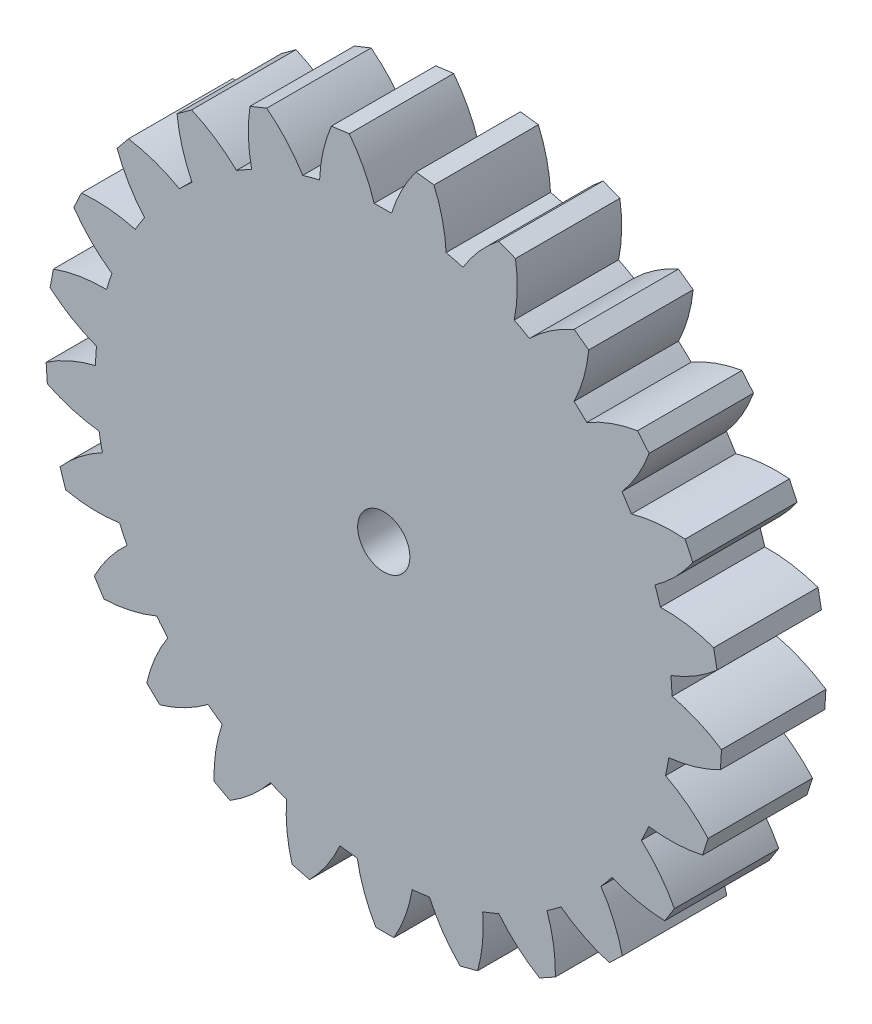
SolidWorks part; units mm, degrees
ref_plane "Front Plane" through (0, 0, 0) normal (0, 0, 1) x (1, 0, 0)
ref_plane "Top Plane" through (0, 0, 0) normal (0, 1, 0) x (1, 0, 0)
ref_plane "Right Plane" through (0, 0, 0) normal (1, 0, 0) x (0, 0, -1)
ref_plane "Plane4"
sketch "Sketch1" plane through (0, 0, 0) normal (0, 0, 1) x (1, 0, 0)
  line L0 (-14.2336, 38.5672) -> (-16.2739, 37.7516)
  line L1 (-4.1952, 40.8953) -> (-6.3742, 40.6127)
  line L2 (6.1069, 40.6538) -> (3.926, 40.922)
  line L3 (16.0252, 37.8579) -> (13.9796, 38.66)
  line L4 (24.9366, 32.6832) -> (23.1547, 33.9689)
  line L5 (32.2811, 25.4549) -> (30.875, 27.1433)
  line L6 (37.5973, 16.6272) -> (36.6553, 18.6123)
  line L7 (40.5512, 6.7547) -> (40.1323, 8.9117)
  line L8 (40.957, -3.5421) -> (41.0878, -1.3488)
  line L9 (38.7894, -13.6165) -> (39.4615, -11.5245)
  line L10 (34.1845, -22.8352) -> (35.3557, -20.9761)
  line L11 (27.4316, -30.6191) -> (29.0284, -29.1097)
  line L12 (18.9551, -36.4791) -> (20.8771, -35.4142)
  line L13 (9.2876, -40.047) -> (11.4141, -39.4936)
  line L14 (-0.9634, -41.0986) -> (1.2338, -41.0914)
  line L15 (-11.154, -39.5678) -> (-9.0239, -40.1073)
  line L16 (-20.6437, -35.5508) -> (-18.7147, -36.6031)
  line L17 (-28.8363, -29.3001) -> (-27.2296, -30.7989)
  line L18 (-35.2169, -21.2083) -> (-34.0335, -23.0596)
  line L19 (-39.3848, -11.7839) -> (-38.699, -13.8714)
  line L20 (-41.078, -1.6191) -> (-40.9328, -3.8115)
  line L21 (-36.7769, 18.3707) -> (-37.7059, 16.3795)
  line L22 (-40.1901, 8.6475) -> (-40.5947, 6.4878)
  line L23 (-23.3777, 33.8158) -> (-25.1511, 32.5184)
  line L24 (-31.0529, 26.9396) -> (-32.4479, 25.2419)
  line L25 (-17.9243, 30.1668) -> (-23.3244, 26.2162)
  line L26 (-24.8633, 24.7614) -> (-29.1113, 19.592)
  line L27 (-30.2401, 17.8003) -> (-33.0691, 11.7368)
  line L28 (-33.7168, 9.7206) -> (-34.949, 3.1441)
  line L29 (-35.075, 1.0302) -> (-34.6329, -5.6461)
  line L30 (-34.2292, -7.725) -> (-32.1407, -14.0816)
  line L31 (-31.2327, -15.9947) -> (-27.629, -21.6322)
  line L32 (-26.2738, -23.2595) -> (-21.3813, -27.8237)
  line L33 (-19.6639, -29.0628) -> (-13.7901, -32.2668)
  line L34 (-11.8185, -33.0399) -> (-5.3324, -34.6826)
  line L35 (-3.2305, -34.9411) -> (3.4604, -34.9191)
  line L36 (5.5605, -34.6467) -> (12.0357, -32.9615)
  line L37 (14.0021, -32.1754) -> (19.8547, -28.9328)
  line L38 (21.5639, -27.6824) -> (26.4262, -23.0861)
  line L39 (27.7707, -21.45) -> (31.3373, -15.7889)
  line L40 (32.2327, -13.8698) -> (34.2793, -7.4996)
  line L41 (34.6693, -5.4181) -> (35.0674, 1.2609)
  line L42 (34.9275, 3.374) -> (33.6521, 9.9422)
  line L43 (32.9911, 11.9541) -> (30.1224, 17.9988)
  line L44 (28.9818, 19.7831) -> (24.6999, 24.9245)
  line L45 (23.1514, 26.3691) -> (17.7254, 30.2841)
  line L46 (15.8663, 31.2982) -> (9.6372, 33.7408)
  line L47 (7.5843, 34.2607) -> (0.9435, 35.0774)
  line L48 (-1.1742, 35.0704) -> (-7.8096, 34.21)
  line L49 (-9.859, 33.6766) -> (-16.0719, 31.1931)
  line L50 (-34.6329, -5.6461) -> (-35.075, 1.0302)
  line L51 (-32.1407, -14.0816) -> (-34.2292, -7.725)
  line L52 (-27.629, -21.6322) -> (-31.2327, -15.9947)
  line L53 (-21.3813, -27.8237) -> (-26.2738, -23.2595)
  line L54 (-13.7901, -32.2668) -> (-19.6639, -29.0628)
  line L55 (-5.3324, -34.6826) -> (-11.8185, -33.0399)
  line L56 (3.4604, -34.9191) -> (-3.2305, -34.9411)
  line L57 (12.0357, -32.9615) -> (5.5605, -34.6467)
  line L58 (19.8547, -28.9328) -> (14.0021, -32.1754)
  line L59 (26.4262, -23.0861) -> (21.5639, -27.6824)
  line L60 (31.3373, -15.7889) -> (27.7707, -21.45)
  line L61 (34.2793, -7.4996) -> (32.2327, -13.8698)
  line L62 (35.0674, 1.2609) -> (34.6693, -5.4181)
  line L63 (33.6521, 9.9422) -> (34.9275, 3.374)
  line L64 (30.1224, 17.9988) -> (32.9911, 11.9541)
  line L65 (24.6999, 24.9245) -> (28.9818, 19.7831)
  line L66 (17.7254, 30.2841) -> (23.1514, 26.3691)
  line L67 (9.6372, 33.7408) -> (15.8663, 31.2982)
  line L68 (0.9435, 35.0774) -> (7.5843, 34.2607)
  line L69 (-7.8096, 34.21) -> (-1.1742, 35.0704)
  line L70 (-16.0719, 31.1931) -> (-9.859, 33.6766)
  line L71 (-23.3244, 26.2162) -> (-17.9243, 30.1668)
  line L72 (-34.949, 3.1441) -> (-33.7168, 9.7206)
  line L73 (-33.0691, 11.7368) -> (-30.2401, 17.8003)
  line L74 (-29.1113, 19.592) -> (-24.8633, 24.7614)
  arc A0 (-16.2739, 37.7516) -> (-16.0719, 31.1931) centre (2.011, 35.0324) ccw
  arc A1 (-9.859, 33.6766) -> (-16.0719, 31.1931) centre (0, 0) ccw
  arc A2 (-9.859, 33.6766) -> (-14.2336, 38.5672) centre (-25.6057, 23.993) ccw
  arc A3 (-6.3742, 40.6127) -> (-7.8096, 34.21) centre (10.66, 33.4317) ccw
  arc A4 (-1.1742, 35.0704) -> (-7.8096, 34.21) centre (0, 0) ccw
  arc A5 (-1.1742, 35.0704) -> (-4.1952, 40.8953) centre (-18.8345, 29.6071) ccw
  arc A6 (3.926, 40.922) -> (0.9435, 35.0774) centre (18.6392, 29.7303) ccw
  arc A7 (7.5843, 34.2607) -> (0.9435, 35.0774) centre (0, 0) ccw
  arc A8 (7.5843, 34.2607) -> (6.1069, 40.6538) centre (-10.8798, 33.3608) ccw
  arc A9 (13.9796, 38.66) -> (9.6372, 33.7408) centre (25.4473, 24.1609) ccw
  arc A10 (15.8663, 31.2982) -> (9.6372, 33.7408) centre (0, 0) ccw
  arc A11 (15.8663, 31.2982) -> (16.0252, 37.8579) centre (-2.2414, 35.0184) ccw
  arc A12 (23.1547, 33.9689) -> (17.7254, 30.2841) centre (30.6564, 17.0734) ccw
  arc A13 (23.1514, 26.3691) -> (17.7254, 30.2841) centre (0, 0) ccw
  arc A14 (23.1514, 26.3691) -> (24.9366, 32.6832) centre (6.5377, 34.4757) ccw
  arc A15 (30.875, 27.1433) -> (24.6999, 24.9245) centre (33.9392, 8.9131) ccw
  arc A16 (28.9818, 19.7831) -> (24.6999, 24.9245) centre (0, 0) ccw
  arc A17 (28.9818, 19.7831) -> (32.2811, 25.4549) centre (14.9061, 31.7667) ccw
  arc A18 (36.6553, 18.6123) -> (30.1224, 17.9988) centre (35.0896, 0.1927) ccw
  arc A19 (32.9911, 11.9541) -> (30.1224, 17.9988) centre (0, 0) ccw
  arc A20 (32.9911, 11.9541) -> (37.5973, 16.6272) centre (22.3378, 27.0617) ccw
  arc A21 (40.1323, 8.9117) -> (33.6521, 9.9422) centre (34.0351, -8.5398) ccw
  arc A22 (34.9275, 3.374) -> (33.6521, 9.9422) centre (0, 0) ccw
  arc A23 (34.9275, 3.374) -> (40.5512, 6.7547) centre (28.366, 20.6563) ccw
  arc A24 (41.0878, -1.3488) -> (35.0674, 1.2609) centre (30.8421, -16.7357) ccw
  arc A25 (34.6693, -5.4181) -> (35.0674, 1.2609) centre (0, 0) ccw
  arc A26 (34.6693, -5.4181) -> (40.957, -3.5421) centre (32.6119, 12.953) ccw
  arc A27 (39.4615, -11.5245) -> (34.2793, -7.4996) centre (25.7111, -23.88) ccw
  arc A28 (32.2327, -13.8698) -> (34.2793, -7.4996) centre (0, 0) ccw
  arc A29 (32.2327, -13.8698) -> (38.7894, -13.6165) centre (34.8086, 4.4358) ccw
  arc A30 (35.3557, -20.9761) -> (31.3373, -15.7889) centre (18.9646, -29.5239) ccw
  arc A31 (27.7707, -21.45) -> (31.3373, -15.7889) centre (0, 0) ccw
  arc A32 (27.7707, -21.45) -> (34.1845, -22.8352) centre (34.8182, -4.3601) ccw
  arc A33 (29.0284, -29.1097) -> (26.4262, -23.0861) centre (11.0265, -33.3126) ccw
  arc A34 (21.5639, -27.6824) -> (26.4262, -23.0861) centre (0, 0) ccw
  arc A35 (21.5639, -27.6824) -> (27.4316, -30.6191) centre (32.64, -12.882) ccw
  arc A36 (20.8771, -35.4142) -> (19.8547, -28.9328) centre (2.3956, -35.0082) ccw
  arc A37 (14.0021, -32.1754) -> (19.8547, -28.9328) centre (0, 0) ccw
  arc A38 (14.0021, -32.1754) -> (18.9551, -36.4791) centre (28.4109, -20.5945) ccw
  arc A39 (11.4141, -39.4936) -> (12.0357, -32.9615) centre (-6.3859, -34.5041) ccw
  arc A40 (5.5605, -34.6467) -> (12.0357, -32.9615) centre (0, 0) ccw
  arc A41 (5.5605, -34.6467) -> (9.2876, -40.047) centre (22.3967, -27.013) ccw
  arc A42 (1.2338, -41.0914) -> (3.4604, -34.9191) centre (-14.7661, -31.832) ccw
  arc A43 (-3.2305, -34.9411) -> (3.4604, -34.9191) centre (0, 0) ccw
  arc A44 (-3.2305, -34.9411) -> (-0.9634, -41.0986) centre (14.9752, -31.7342) ccw
  arc A45 (-9.0239, -40.1073) -> (-5.3324, -34.6826) centre (-22.2185, -27.1598) ccw
  arc A46 (-11.8185, -33.0399) -> (-5.3324, -34.6826) centre (0, 0) ccw
  arc A47 (-11.8185, -33.0399) -> (-11.154, -39.5678) centre (6.6127, -34.4614) ccw
  arc A48 (-18.7147, -36.6031) -> (-13.7901, -32.2668) centre (-28.2748, -20.781) ccw
  arc A49 (-19.6639, -29.0628) -> (-13.7901, -32.2668) centre (0, 0) ccw
  arc A50 (-19.6639, -29.0628) -> (-20.6437, -35.5508) centre (-2.1652, -35.0232) ccw
  arc A51 (-27.2296, -30.7989) -> (-21.3813, -27.8237) centre (-32.5545, -13.0965) ccw
  arc A52 (-26.2738, -23.2595) -> (-21.3813, -27.8237) centre (0, 0) ccw
  arc A53 (-26.2738, -23.2595) -> (-28.8363, -29.3001) centre (-10.8071, -33.3845) ccw
  arc A54 (-34.0335, -23.0596) -> (-27.629, -21.6322) centre (-34.7887, -4.5891) ccw
  arc A55 (-31.2327, -15.9947) -> (-27.629, -21.6322) centre (0, 0) ccw
  arc A56 (-31.2327, -15.9947) -> (-35.2169, -21.2083) centre (-18.77, -29.648) ccw
  arc A57 (-38.699, -13.8714) -> (-32.1407, -14.0816) centre (-34.837, 4.2067) ccw
  arc A58 (-34.2292, -7.725) -> (-32.1407, -14.0816) centre (0, 0) ccw
  arc A59 (-34.2292, -7.725) -> (-39.3848, -11.7839) centre (-25.5534, -24.0487) ccw
  arc A60 (-40.9328, -3.8115) -> (-34.6329, -5.6461) centre (-32.6964, 12.7382) ccw
  arc A61 (-35.075, 1.0302) -> (-34.6329, -5.6461) centre (0, 0) ccw
  arc A62 (-35.075, 1.0302) -> (-41.078, -1.6191) centre (-30.7313, -16.9382) ccw
  arc A63 (-37.7059, 16.3795) -> (-33.0691, 11.7368) centre (-22.5154, 26.9142) ccw
  arc A64 (-30.2401, 17.8003) -> (-33.0691, 11.7368) centre (0, 0) ccw
  arc A65 (-30.2401, 17.8003) -> (-36.7769, 18.3707) centre (-35.0901, -0.0382) ccw
  arc A66 (-40.5947, 6.4878) -> (-34.949, 3.1441) centre (-28.5013, 20.4692) ccw
  arc A67 (-33.7168, 9.7206) -> (-34.949, 3.1441) centre (0, 0) ccw
  arc A68 (-33.7168, 9.7206) -> (-40.1901, 8.6475) centre (-33.9782, -8.7635) ccw
  arc A69 (-25.1511, 32.5184) -> (-23.3244, 26.2162) centre (-6.7644, 34.4319) ccw
  arc A70 (-17.9243, 30.1668) -> (-23.3244, 26.2162) centre (0, 0) ccw
  arc A71 (-17.9243, 30.1668) -> (-23.3777, 33.8158) centre (-30.7681, 16.8713) ccw
  arc A72 (-32.4479, 25.2419) -> (-29.1113, 19.592) centre (-15.1148, 31.668) ccw
  arc A73 (-24.8633, 24.7614) -> (-29.1113, 19.592) centre (0, 0) ccw
  arc A74 (-24.8633, 24.7614) -> (-31.0529, 26.9396) centre (-33.9972, 8.6896) ccw
  arc A75 (-16.0719, 31.1931) -> (-17.9243, 30.1668) centre (0, 0) ccw
  arc A76 (-23.3244, 26.2162) -> (-24.8633, 24.7614) centre (0, 0) ccw
  arc A77 (-29.1113, 19.592) -> (-30.2401, 17.8003) centre (0, 0) ccw
  arc A78 (-33.0691, 11.7368) -> (-33.7168, 9.7206) centre (0, 0) ccw
  arc A79 (-34.949, 3.1441) -> (-35.075, 1.0302) centre (0, 0) ccw
  arc A80 (-34.6329, -5.6461) -> (-34.2292, -7.725) centre (0, 0) ccw
  arc A81 (-32.1407, -14.0816) -> (-31.2327, -15.9947) centre (0, 0) ccw
  arc A82 (-27.629, -21.6322) -> (-26.2738, -23.2595) centre (0, 0) ccw
  arc A83 (-21.3813, -27.8237) -> (-19.6639, -29.0628) centre (0, 0) ccw
  arc A84 (-13.7901, -32.2668) -> (-11.8185, -33.0399) centre (0, 0) ccw
  arc A85 (-5.3324, -34.6826) -> (-3.2305, -34.9411) centre (0, 0) ccw
  arc A86 (3.4604, -34.9191) -> (5.5605, -34.6467) centre (0, 0) ccw
  arc A87 (12.0357, -32.9615) -> (14.0021, -32.1754) centre (0, 0) ccw
  arc A88 (19.8547, -28.9328) -> (21.5639, -27.6824) centre (0, 0) ccw
  arc A89 (26.4262, -23.0861) -> (27.7707, -21.45) centre (0, 0) ccw
  arc A90 (31.3373, -15.7889) -> (32.2327, -13.8698) centre (0, 0) ccw
  arc A91 (34.2793, -7.4996) -> (34.6693, -5.4181) centre (0, 0) ccw
  arc A92 (35.0674, 1.2609) -> (34.9275, 3.374) centre (0, 0) ccw
  arc A93 (33.6521, 9.9422) -> (32.9911, 11.9541) centre (0, 0) ccw
  arc A94 (30.1224, 17.9988) -> (28.9818, 19.7831) centre (0, 0) ccw
  arc A95 (24.6999, 24.9245) -> (23.1514, 26.3691) centre (0, 0) ccw
  arc A96 (17.7254, 30.2841) -> (15.8663, 31.2982) centre (0, 0) ccw
  arc A97 (9.6372, 33.7408) -> (7.5843, 34.2607) centre (0, 0) ccw
  arc A98 (0.9435, 35.0774) -> (-1.1742, 35.0704) centre (0, 0) ccw
  arc A99 (-7.8096, 34.21) -> (-9.859, 33.6766) centre (0, 0) ccw
  circle A100 centre (0, 0) radius 3.175
  arc A101 (-35.075, 1.0302) -> (-34.6329, -5.6461) centre (0, 0) ccw
  arc A102 (-34.2292, -7.725) -> (-32.1407, -14.0816) centre (0, 0) ccw
  arc A103 (-31.2327, -15.9947) -> (-27.629, -21.6322) centre (0, 0) ccw
  arc A104 (-26.2738, -23.2595) -> (-21.3813, -27.8237) centre (0, 0) ccw
  arc A105 (-19.6639, -29.0628) -> (-13.7901, -32.2668) centre (0, 0) ccw
  arc A106 (-11.8185, -33.0399) -> (-5.3324, -34.6826) centre (0, 0) ccw
  arc A107 (-3.2305, -34.9411) -> (3.4604, -34.9191) centre (0, 0) ccw
  arc A108 (5.5605, -34.6467) -> (12.0357, -32.9615) centre (0, 0) ccw
  arc A109 (14.0021, -32.1754) -> (19.8547, -28.9328) centre (0, 0) ccw
  arc A110 (21.5639, -27.6824) -> (26.4262, -23.0861) centre (0, 0) ccw
  arc A111 (27.7707, -21.45) -> (31.3373, -15.7889) centre (0, 0) ccw
  arc A112 (32.2327, -13.8698) -> (34.2793, -7.4996) centre (0, 0) ccw
  arc A113 (34.6693, -5.4181) -> (35.0674, 1.2609) centre (0, 0) ccw
  arc A114 (34.9275, 3.374) -> (33.6521, 9.9422) centre (0, 0) ccw
  arc A115 (32.9911, 11.9541) -> (30.1224, 17.9988) centre (0, 0) ccw
  arc A116 (28.9818, 19.7831) -> (24.6999, 24.9245) centre (0, 0) ccw
  arc A117 (23.1514, 26.3691) -> (17.7254, 30.2841) centre (0, 0) ccw
  arc A118 (15.8663, 31.2982) -> (9.6372, 33.7408) centre (0, 0) ccw
  arc A119 (7.5843, 34.2607) -> (0.9435, 35.0774) centre (0, 0) ccw
  arc A120 (-1.1742, 35.0704) -> (-7.8096, 34.21) centre (0, 0) ccw
  arc A121 (-9.859, 33.6766) -> (-16.0719, 31.1931) centre (0, 0) ccw
  arc A122 (-17.9243, 30.1668) -> (-23.3244, 26.2162) centre (0, 0) ccw
  arc A123 (-33.7168, 9.7206) -> (-34.949, 3.1441) centre (0, 0) ccw
  arc A124 (-30.2401, 17.8003) -> (-33.0691, 11.7368) centre (0, 0) ccw
  arc A125 (-24.8633, 24.7614) -> (-29.1113, 19.592) centre (0, 0) ccw
  dimension "D1" = 6.35
  dimension "D2" = 37.4739
  dimension "D3" = 8.1212
extrude "Extrusion2" add sketch "Sketch1" along normal blind 12.7 contours A1 A2 L0 A0 | A4 A5 L1 A3 | A7 A8 L2 A6 | A10 A11 L3 A9 | A13 A14 L4 A12 | A16 A17 L5 A15 | A19 A20 L6 A18 | A22 A23 L7 A21 | A25 A26 L8 A24 | A28 A29 L9 A27 | A31 A32 L10 A30 | A34 A35 L11 A33 | A37 A38 L12 A36 | A40 A41 L13 A39 | A43 A44 L14 A42 | A46 A47 L15 A45 | A49 A50 L16 A48 | A52 A53 L17 A51 | A55 A56 L18 A54 | A58 A59 L19 A57 | A61 A62 L20 A60 | A64 A65 L21 A63 | A67 A68 L22 A66 | A70 A71 L23 A69 | A73 A74 L24 A72 | L48 A99 L49 A75 L25 A76 L26 A77 L27 A78 L28 A79 L29 A80 L30 A81 L31 A82 L32 A83 L33 A84 L34 A85 L35 A86 L36 A87 L37 A88 L38 A89 L39 A90 L40 A91 L41 A92 L42 A93 L43 A94 L44 A95 L45 A96 L46 A97 L47 A98 | L29 A61 | L30 A58 | L31 A55 | L32 A52 | L33 A49 | L34 A46 | L35 A43 | L36 A40 | L37 A37 | L38 A34 | L39 A31 | L40 A28 | L41 A25 | L42 A22 | L43 A19 | L44 A16 | L45 A13 | L46 A10 | L47 A7 | L48 A4 | L49 A1 | L25 A70 | L28 A67 | L27 A64 | L26 A73
